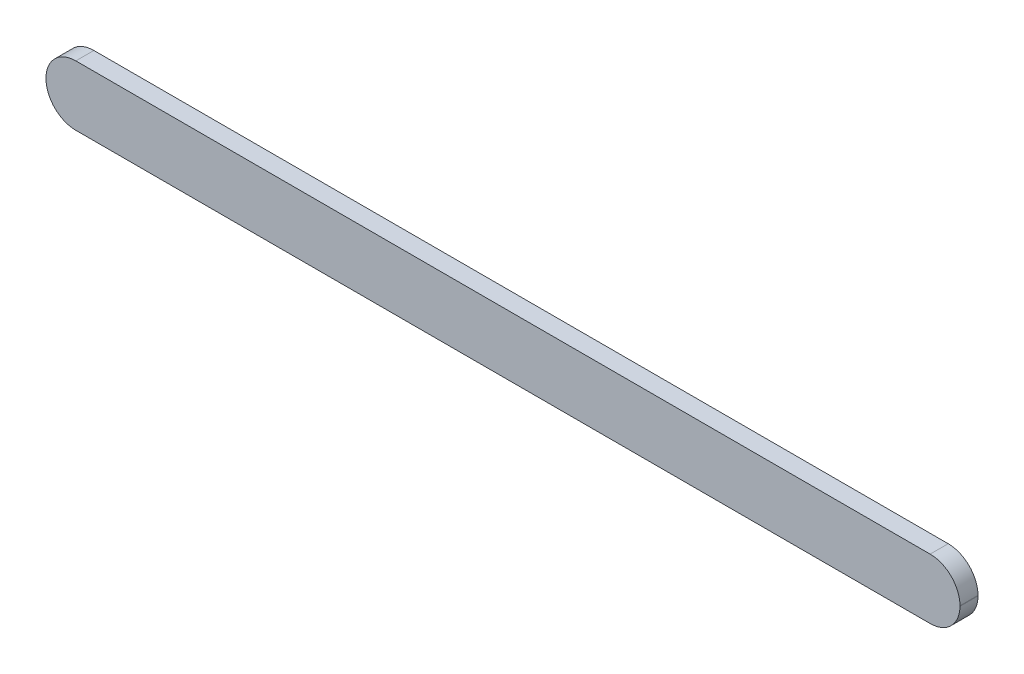
SolidWorks part; units mm, degrees
ref_plane "Front Plane" through (0, 0, 0) normal (0, 0, 1) x (1, 0, 0)
ref_plane "Top Plane" through (0, 0, 0) normal (0, 1, 0) x (1, 0, 0)
ref_plane "Right Plane" through (0, 0, 0) normal (1, 0, 0) x (0, 0, -1)
sketch "Sketch2" plane through (0, 0, 0) normal (0, 0, 1) x (1, 0, 0)
  line L1 (31.496, 0) -> (933.704, 0)
  line L2 (0, -31.496) -> (0, -32.004)
  line L3 (31.496, -63.5) -> (933.704, -63.5)
  line L4 (965.2, -31.496) -> (965.2, -32.004)
  arc A0 (965.2, -32.004) -> (933.704, -63.5) centre (933.704, -32.004) cw
  arc A1 (965.2, -31.496) -> (933.704, 0) centre (933.704, -31.496) ccw
  arc A2 (0, -32.004) -> (31.496, -63.5) centre (31.496, -32.004) ccw
  arc A3 (0, -31.496) -> (31.496, 0) centre (31.496, -31.496) cw
  point P9 (965.2, 0)
  point P14 (0, 0)
  dimension "D3" = 31.496
  dimension "D1" = 63.5
  dimension "D2" = 965.2
extrude "Boss-Extrude1" add sketch "Sketch2" along normal blind 19.05
sketch "Sketch3" plane through (0, 0, 0) normal (0, 0, 1) x (1, 0, 0)
  line L0 (965.2, -31.75) -> (0, -31.75) construction
  line L1 (965.2, -32.004) -> (965.2, -31.496) construction
  line L2 (0, -31.496) -> (0, -32.004) construction
  line L3 (844.55, 16.355) -> (844.55, -92.9933) construction
  line L4 (723.9, 16.355) -> (723.9, -92.9933) construction
  line L5 (603.25, 16.355) -> (603.25, -92.9933) construction
  line L6 (482.6, 16.355) -> (482.6, -92.9933) construction
  line L7 (361.95, 16.355) -> (361.95, -92.9933) construction
  line L8 (241.3, 16.355) -> (241.3, -92.9933) construction
  line L9 (120.65, 16.355) -> (120.65, -92.9933) construction
  circle A0 centre (844.55, -31.75) radius 16.6687
  circle A1 centre (723.9, -31.75) radius 16.6687
  circle A2 centre (603.25, -31.75) radius 16.6687
  circle A3 centre (482.6, -31.75) radius 16.6687
  circle A4 centre (361.95, -31.75) radius 16.6687
  circle A5 centre (241.3, -31.75) radius 16.6687
  circle A6 centre (120.65, -31.75) radius 16.6687
  dimension "D3" = 7
  dimension "D1" = 120.65
  dimension "D2" = 7
extrude "Cut-Extrude1" cut sketch "Sketch3" along normal blind 9.525
